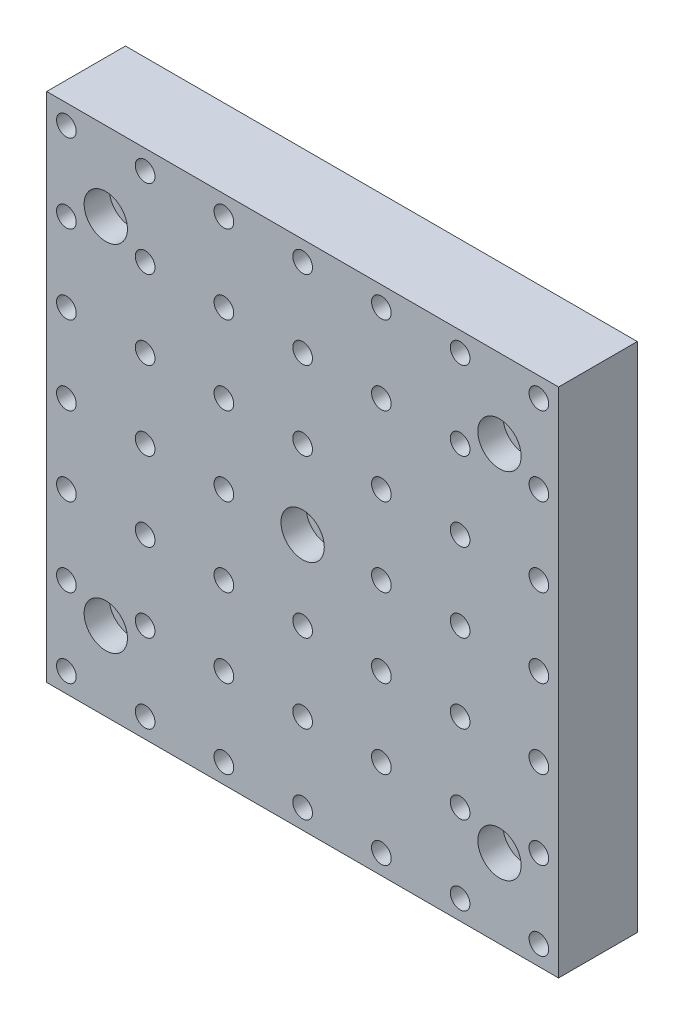
SolidWorks part; units mm, degrees
material "1023 Листовая углеродистая сталь (SS)"
ref_plane "Front" through (0, 0, 0) normal (0, 0, 1) x (1, 0, 0)
ref_plane "Top" through (0, 0, 0) normal (0, 1, 0) x (1, 0, 0)
ref_plane "Right" through (0, 0, 0) normal (1, 0, 0) x (0, 0, -1)
sketch "Sketch1" plane through (0, 0, 0) normal (0, 0, 1) x (1, 0, 0)
  line L1 (-65, 65) -> (65, 65)
  line L2 (-65, 65) -> (-65, -65)
  line L3 (-65, -65) -> (65, -65)
  line L4 (65, 65) -> (65, -65)
  line L5 (-65, 65) -> (65, -65) construction
  line L6 (-65, -65) -> (65, 65) construction
  point P0 (0, 0)
  dimension "D1" = 130
extrude "Extrude1" add sketch "Sketch1" along normal blind 20
hole_wizard "M6 Tapped Hole1" positions "Sketch2" profile "Sketch3" tap size "M6" standard "DIN" end condition through all
sketch "Sketch2" plane through (0, 0, 20) normal (0, 0, 1) x (1, 0, 0)
  line L0 (-65, 65) -> (-65, -65) construction
  line L1 (-65, -65) -> (65, -65) construction
  point P0 (-60, -60)
  point P14 (-40, -60)
  point P15 (-20, -60)
  point P16 (0, -60)
  point P17 (20, -60)
  point P18 (40, -60)
  point P19 (-40, -40)
  point P20 (-20, -40)
  point P21 (0, -40)
  point P22 (20, -40)
  point P23 (40, -40)
  point P24 (-40, -20)
  point P25 (-20, -20)
  point P26 (0, -20)
  point P27 (20, -20)
  point P28 (40, -20)
  point P29 (-40, 0)
  point P30 (-20, 0)
  point P31 (0, 0)
  point P32 (20, 0)
  point P33 (40, 0)
  point P34 (-40, 20)
  point P35 (-20, 20)
  point P36 (0, 20)
  point P37 (20, 20)
  point P38 (40, 20)
  point P39 (-40, 40)
  point P40 (-20, 40)
  point P41 (0, 40)
  point P42 (20, 40)
  point P43 (40, 40)
  point P44 (-40, 60)
  point P45 (-20, 60)
  point P46 (0, 60)
  point P47 (20, 60)
  point P48 (40, 60)
  point P49 (-60, -40)
  point P50 (-60, -20)
  point P51 (-60, 0)
  point P52 (-60, 20)
  point P53 (-60, 40)
  point P54 (-60, 60)
  point P55 (60, -60)
  point P56 (60, -40)
  point P57 (60, -20)
  point P58 (60, 0)
  point P59 (60, 20)
  point P60 (60, 40)
  point P61 (60, 60)
  dimension "5" = 5
  dimension "D2" = 5
  dimension "D3" = 7
  dimension "D4" = 7
sketch "Sketch3" plane through (-60, -60, 20) normal (1, 0, 0) x (0, -1, 0)
  line L0 (0, 0) -> (0, 20)
  line L1 (0, 20) -> (2.5, 20)
  line L2 (2.5, 20) -> (2.5, 0)
  line L5 (2.5, 0) -> (0, 0)
  line L11 (0, -6.35) -> (0, 107.95) construction
  dimension "Диаметр проходного сверла" = 5
  dimension "Глубина проходного сверла" = 20
cosmetic thread "Cosmetic Thread1" parameters "D2"=6
cosmetic thread "Cosmetic Thread2" parameters "D2"=6
cosmetic thread "Cosmetic Thread3" parameters "D2"=6
cosmetic thread "Cosmetic Thread4" parameters "D2"=6
cosmetic thread "Cosmetic Thread5" parameters "D2"=6
cosmetic thread "Cosmetic Thread6" parameters "D2"=6
cosmetic thread "Cosmetic Thread7" parameters "D2"=6
cosmetic thread "Cosmetic Thread8" parameters "D2"=6
cosmetic thread "Cosmetic Thread9" parameters "D2"=6
cosmetic thread "Cosmetic Thread10" parameters "D2"=6
cosmetic thread "Cosmetic Thread11" parameters "D2"=6
cosmetic thread "Cosmetic Thread12" parameters "D2"=6
cosmetic thread "Cosmetic Thread13" parameters "D2"=6
cosmetic thread "Cosmetic Thread14" parameters "D2"=6
cosmetic thread "Cosmetic Thread15" parameters "D2"=6
cosmetic thread "Cosmetic Thread16" parameters "D2"=6
cosmetic thread "Cosmetic Thread17" parameters "D2"=6
cosmetic thread "Cosmetic Thread18" parameters "D2"=6
cosmetic thread "Cosmetic Thread19" parameters "D2"=6
cosmetic thread "Cosmetic Thread20" parameters "D2"=6
cosmetic thread "Cosmetic Thread21" parameters "D2"=6
cosmetic thread "Cosmetic Thread22" parameters "D2"=6
cosmetic thread "Cosmetic Thread23" parameters "D2"=6
cosmetic thread "Cosmetic Thread24" parameters "D2"=6
cosmetic thread "Cosmetic Thread25" parameters "D2"=6
cosmetic thread "Cosmetic Thread26" parameters "D2"=6
cosmetic thread "Cosmetic Thread27" parameters "D2"=6
cosmetic thread "Cosmetic Thread28" parameters "D2"=6
cosmetic thread "Cosmetic Thread29" parameters "D2"=6
cosmetic thread "Cosmetic Thread30" parameters "D2"=6
cosmetic thread "Cosmetic Thread32" parameters "D2"=6
cosmetic thread "Cosmetic Thread33" parameters "D2"=6
cosmetic thread "Cosmetic Thread34" parameters "D2"=6
cosmetic thread "Cosmetic Thread35" parameters "D2"=6
cosmetic thread "Cosmetic Thread36" parameters "D2"=6
cosmetic thread "Cosmetic Thread37" parameters "D2"=6
cosmetic thread "Cosmetic Thread38" parameters "D2"=6
cosmetic thread "Cosmetic Thread39" parameters "D2"=6
cosmetic thread "Cosmetic Thread40" parameters "D2"=6
cosmetic thread "Cosmetic Thread41" parameters "D2"=6
cosmetic thread "Cosmetic Thread42" parameters "D2"=6
cosmetic thread "Cosmetic Thread43" parameters "D2"=6
cosmetic thread "Cosmetic Thread44" parameters "D2"=6
cosmetic thread "Cosmetic Thread45" parameters "D2"=6
cosmetic thread "Cosmetic Thread46" parameters "D2"=6
cosmetic thread "Cosmetic Thread47" parameters "D2"=6
cosmetic thread "Cosmetic Thread48" parameters "D2"=6
cosmetic thread "Cosmetic Thread49" parameters "D2"=6
hole_wizard "CBORE for M6 Hex Socket Head Cap Screw1" positions "Sketch4" profile "Sketch5" counterbore size "M6" standard "DIN" end condition through all
sketch "Sketch4" plane through (0, 0, 20) normal (0, 0, 1) x (1, 0, 0)
  line L1 (50, 45) -> (-50, 45)
  line L2 (50, 45) -> (50, -45)
  line L3 (50, -45) -> (-50, -45)
  line L4 (-50, 45) -> (-50, -45)
  line L5 (50, 45) -> (-50, -45) construction
  line L6 (50, -45) -> (-50, 45) construction
  point P0 (-50, 45)
  point P2 (50, 45)
  point P4 (50, -45)
  point P6 (-50, -45)
  point P10 (0, 0)
  point P53 (-50, 45)
  point P54 (50, 45)
  point P55 (50, -45)
  dimension "D1" = 90
  dimension "D2" = 100
sketch "Sketch5" plane through (-50, 45, 20) normal (1, 0, 0) x (0, -1, 0)
  line L0 (0, 0) -> (0, 20)
  line L1 (0, 20) -> (3.3, 20)
  line L3 (3.3, 20) -> (3.3, 6.4)
  line L4 (3.3, 6.4) -> (5.5, 6.4)
  line L5 (5.5, 6.4) -> (5.5, 0)
  line L7 (5.5, 0) -> (0, 0)
  line L11 (0, -6.35) -> (0, 107.95) construction
  dimension "Диаметр сквозного отверстия" = 6.6
  dimension "Глубина сквозного отверстия" = 20
  dimension "Диаметр цековки" = 11
  dimension "Глубина цековки" = 6.4
